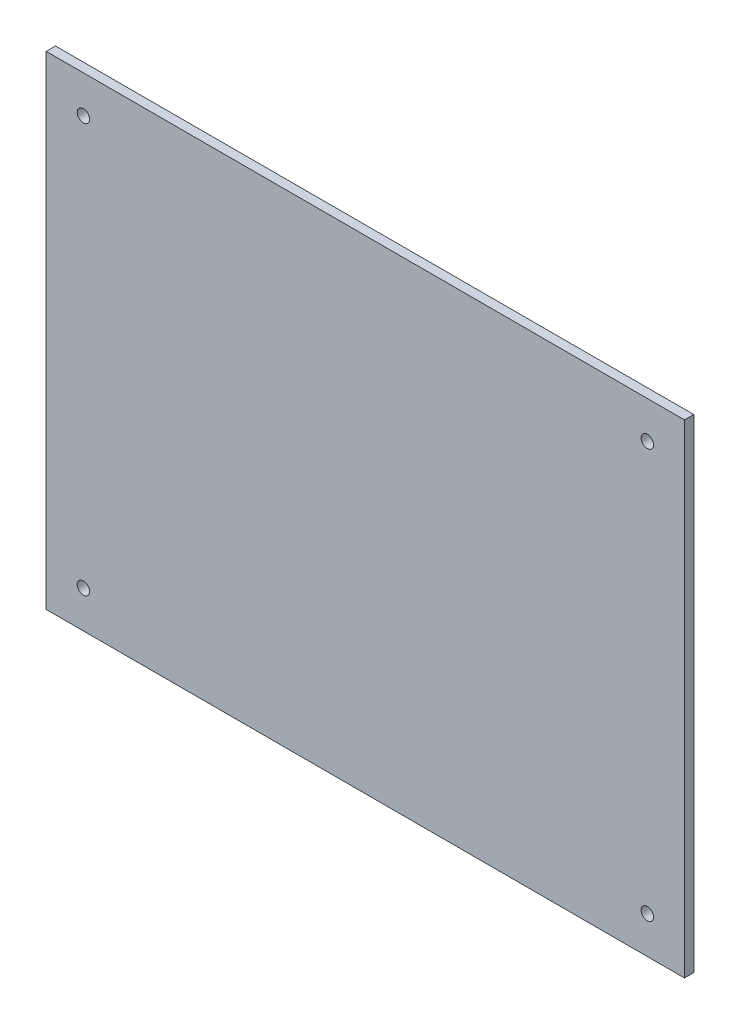
SolidWorks part; units mm, degrees
ref_plane "Plan de face" through (0, 0, 0) normal (0, 0, 1) x (1, 0, 0)
ref_plane "Plan de dessus" through (0, 0, 0) normal (0, 1, 0) x (1, 0, 0)
ref_plane "Plan de droite" through (0, 0, 0) normal (1, 0, 0) x (0, 0, -1)
sketch "Esquisse1" plane through (0, 0, 0) normal (0, 0, 1) x (1, 0, 0)
  line L1 (0, 0) -> (206, 0)
  line L2 (0, 0) -> (0, 156)
  line L3 (0, 156) -> (206, 156)
  line L4 (206, 0) -> (206, 156)
  dimension "D1" = 206
  dimension "D2" = 156
extrude "Boss.-Extru.1" add sketch "Esquisse1" along normal blind 3
sketch "Esquisse2" plane through (0, 0, 3) normal (0, 0, 1) x (1, 0, 0)
  line L0 (103, 156) -> (103, 0) construction
  line L1 (206, 156) -> (0, 156) construction
  line L2 (0, 0) -> (206, 0) construction
  line L3 (0, 78) -> (206, 78) construction
  line L4 (0, 156) -> (0, 0) construction
  line L5 (206, 0) -> (206, 156) construction
  circle A0 centre (12, 144) radius 2
  circle A1 centre (194, 144) radius 2
  circle A2 centre (194, 12) radius 2
  circle A3 centre (12, 12) radius 2
  dimension "D1" = 12
  dimension "D2" = 12
  dimension "D3" = 4
extrude "Enlèv. mat.-Extru.1" cut sketch "Esquisse2" against normal blind 3
